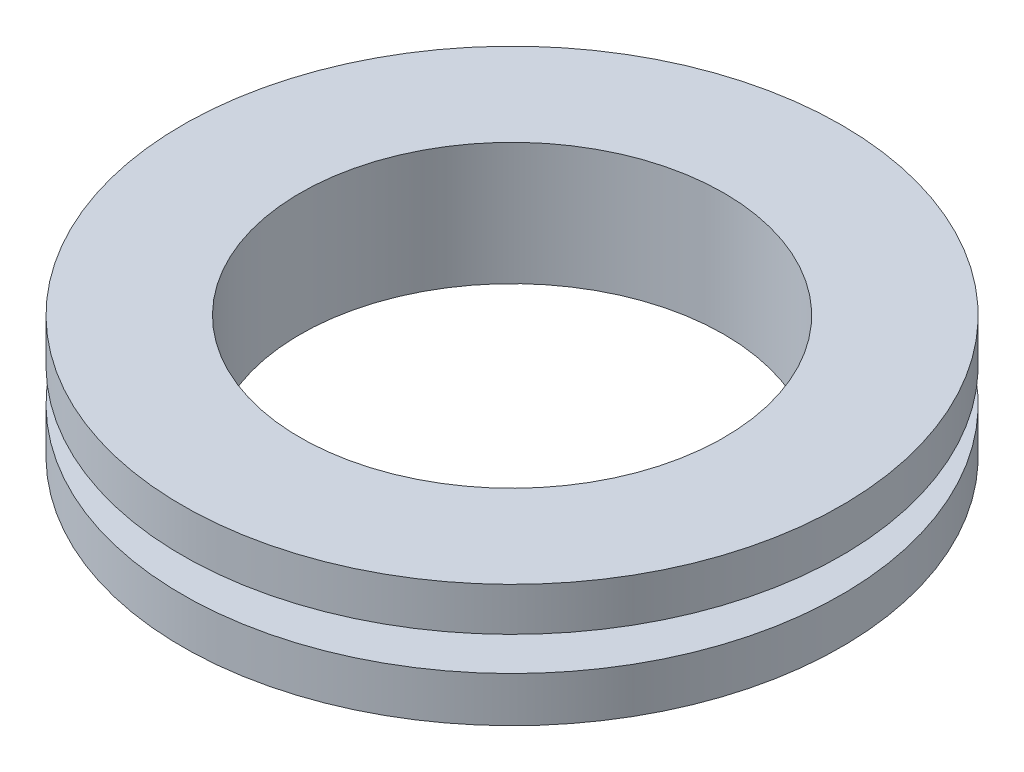
SolidWorks part; units mm, degrees
ref_plane "Front" through (0, 0, 0) normal (0, 0, 1) x (1, 0, 0)
ref_plane "Top" through (0, 0, 0) normal (0, 1, 0) x (1, 0, 0)
ref_plane "Right" through (0, 0, 0) normal (1, 0, 0) x (0, 0, -1)
sketch "Sketch1" plane through (0, 0, 0) normal (0, 0, 1) x (1, 0, 0)
  line L0 (0, 0) -> (0, 32.5) construction
  line L1 (17.5, 2.4) -> (14.75, 2.4)
  line L2 (11.25, 0) -> (17.5, 0)
  line L3 (11.25, 0) -> (11.25, 6.5)
  line L4 (11.25, 6.5) -> (17.5, 6.5)
  line L5 (17.5, 0) -> (17.5, 2.4)
  line L6 (14.75, 2.4) -> (14.75, 4.2)
  line L7 (14.75, 4.2) -> (17.5, 4.2)
  line L8 (17.5, 4.2) -> (17.5, 6.5)
  dimension "D1" = 6.5
  dimension "D2" = 22.5
  dimension "D3" = 35
  dimension "D4" = 2.3
  dimension "D5" = 1.8
  dimension "D6" = 29.5
revolve "Revolve1" add sketch "Sketch1" angle 360 about L0
